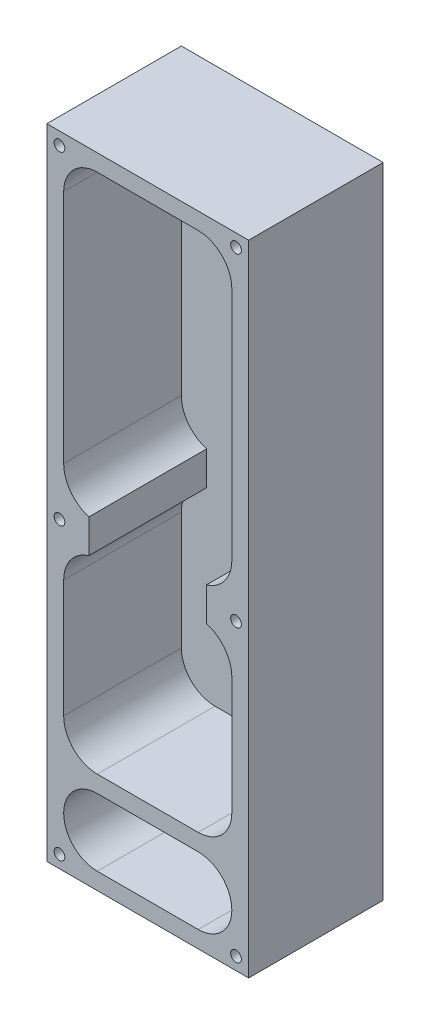
SolidWorks part; units mm, degrees
ref_plane "Front Plane" through (0, 0, 0) normal (0, 0, 1) x (1, 0, 0)
ref_plane "Top Plane" through (0, 0, 0) normal (0, 1, 0) x (1, 0, 0)
ref_plane "Right Plane" through (0, 0, 0) normal (1, 0, 0) x (0, 0, -1)
sketch "Sketch1" plane through (0, 0, 0) normal (0, 0, 1) x (1, 0, 0)
  line L1 (0, 0) -> (76.2, 0)
  line L2 (0, 0) -> (0, -241.3)
  line L3 (0, -241.3) -> (76.2, -241.3)
  line L4 (76.2, 0) -> (76.2, -241.3)
  line L5 (6.35, -6.35) -> (69.85, -6.35)
  line L6 (6.35, -6.35) -> (6.35, -234.95)
  line L7 (6.35, -234.95) -> (69.85, -234.95)
  line L8 (69.85, -6.35) -> (69.85, -234.95)
  dimension "D1" = 241.3
  dimension "D2" = 76.2
  dimension "D3" = 228.6
  dimension "D4" = 6.35
  dimension "D5" = 6.35
  dimension "D6" = 63.5
extrude "Boss-Extrude1" add sketch "Sketch1" along normal blind 44.45
fillet "Fillet1" radius 12.7 4 edges at (6.35, -234.95, 22.225) (69.85, -234.95, 22.225) (69.85, -6.35, 22.225) (6.35, -6.35, 22.225)
sketch "Sketch2" plane through (0, 0, 0) normal (0, 0, -1) x (-1, 0, 0)
  line L1 (0, 0) -> (-76.2, 0)
  line L2 (0, 0) -> (0, -241.3)
  line L3 (0, -241.3) -> (-76.2, -241.3)
  line L4 (-76.2, 0) -> (-76.2, -241.3)
extrude "Boss-Extrude2" add sketch "Sketch2" along normal blind 6.35
ref_plane "Plane1" through (38.1, 0, 0) normal (-1, 0, 0) x (0, 0, 1)
sketch "Sketch3" plane through (0, 0, 44.45) normal (0, 0, 1) x (1, 0, 0)
  line L0 (69.85, -222.25) -> (69.85, -19.05) construction
  line L4 (60.325, -120.65) -> (60.325, -133.35)
  line L6 (69.85, -107.95) -> (69.85, -146.05)
  line L7 (69.85, -222.25) -> (69.85, -19.05) construction
  line L8 (19.05, -234.95) -> (57.15, -234.95) construction
  arc A0 (69.85, -107.95) -> (60.325, -120.65) centre (56.6208, -107.95) cw
  arc A1 (69.85, -146.05) -> (60.325, -133.35) centre (56.6208, -146.05) ccw
  dimension "D4" = 38.1
  dimension "D5" = 13.2292
  dimension "D1" = 12.7
  dimension "D2" = 9.525
  dimension "D3" = 101.6
extrude "Boss-Extrude3" add sketch "Sketch3" against normal up to surface (44.45 mm away) up to face at (38.1, -120.65, 0)
mirror "Mirror1" about plane through (38.1, 0, 0) normal (-1, 0, 0) of "Boss-Extrude3"
sketch "Sketch4" plane through (0, 0, 44.45) normal (0, 0, 1) x (1, 0, 0)
  line L0 (4.7625, -4.7625) -> (4.7625, -236.5375) construction
  line L1 (4.7625, -236.5375) -> (71.4375, -236.5375) construction
  line L2 (71.4375, -236.5375) -> (71.4375, -4.7625) construction
  line L3 (71.4375, -4.7625) -> (4.7625, -4.7625) construction
  line L4 (76.2, 0) -> (0, 0) construction
  line L5 (0, -241.3) -> (76.2, -241.3) construction
  line L6 (0, 0) -> (0, -241.3) construction
  line L7 (76.2, -241.3) -> (76.2, 0) construction
  line L8 (19.05, -234.95) -> (57.15, -234.95) construction
  point P12 (71.4375, -127)
  point P13 (4.7625, -127)
  point P17 (71.4375, -4.7625)
  point P18 (4.7625, -4.7625)
  point P19 (71.4375, -236.5375)
  point P20 (4.7625, -236.5375)
  dimension "D1" = 4.7625
  dimension "D2" = 4.7625
  dimension "D3" = 4.7625
  dimension "D4" = 4.7625
  dimension "D5" = 107.95
hole_wizard "#10-32 Tapped Hole1" positions "Sketch5" profile "Sketch7" tap size "#10-32" standard "ANSI Inch" end condition through all
sketch "Sketch5" plane through (0, 0, 44.45) normal (0, 0, 1) x (1, 0, 0)
  point P0 (4.7625, -4.7625)
  point P3 (71.4375, -4.7625)
  point P6 (71.4375, -127)
  point P9 (4.7625, -127)
  point P12 (4.7625, -236.5375)
  point P15 (71.4375, -236.5375)
sketch "Sketch7" plane through (4.7625, -4.7625, 44.45) normal (1, 0, 0) x (0, -1, 0)
  line L0 (0, 0) -> (0, 50.8)
  line L1 (0, 50.8) -> (2.0193, 50.8)
  line L2 (2.0193, 50.8) -> (2.0193, 0)
  line L5 (2.0193, 0) -> (0, 0)
  line L11 (0, -6.35) -> (0, 107.95) construction
  dimension "Thru Tap Drill Dia." = 4.0386
  dimension "Thru Tap Drill Depth" = 50.8
cosmetic thread "Hole Thread1" parameters "D2"=4.826
cosmetic thread "Hole Thread2" parameters "D2"=4.826
cosmetic thread "Hole Thread3" parameters "D2"=4.826
cosmetic thread "Hole Thread4" parameters "D2"=4.826
cosmetic thread "Hole Thread5" parameters "D2"=4.826
cosmetic thread "Hole Thread6" parameters "D2"=4.826
sketch "Sketch8" plane through (0, 0, 44.45) normal (0, 0, 1) x (1, 0, 0)
  line L0 (19.05, -209.55) -> (57.15, -209.55)
  line L1 (6.35, -146.05) -> (6.35, -222.25) construction
  line L3 (6.35, -190.5) -> (6.35, -222.25)
  line L4 (69.85, -222.25) -> (69.85, -146.05) construction
  line L5 (19.05, -203.2) -> (57.15, -203.2)
  line L6 (69.85, -190.5) -> (69.85, -222.25)
  arc A0 (6.35, -222.25) -> (19.05, -209.55) centre (19.05, -222.25) cw
  arc A1 (6.35, -190.5) -> (19.05, -203.2) centre (19.05, -190.5) ccw
  arc A2 (69.85, -190.5) -> (57.15, -203.2) centre (57.15, -190.5) cw
  arc A3 (69.85, -222.25) -> (57.15, -209.55) centre (57.15, -222.25) ccw
  dimension "D4" = 12.7
  dimension "D6" = 12.7
  dimension "D7" = 12.7
  dimension "D8" = 12.7
  dimension "D1" = 12.7
  dimension "D2" = 6.35
  dimension "D3" = 38.1
extrude "Boss-Extrude4" add sketch "Sketch8" against normal up to surface (44.45 mm away) up to face at (38.1, -123.825, 0)
